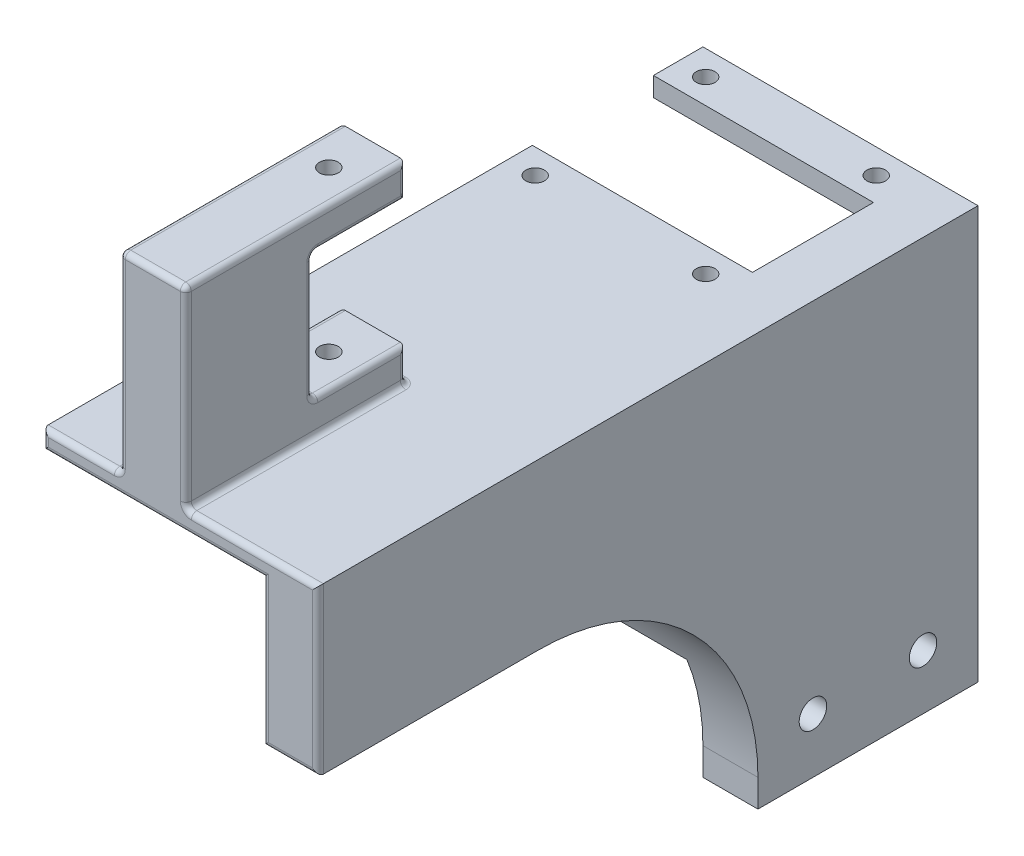
SolidWorks part; units mm, degrees
ref_plane "Front Plane" through (0, 0, 0) normal (0, 0, 1) x (1, 0, 0)
ref_plane "Top Plane" through (0, 0, 0) normal (0, 1, 0) x (1, 0, 0)
ref_plane "Right Plane" through (0, 0, 0) normal (1, 0, 0) x (0, 0, -1)
sketch "Sketch1" plane through (0, 0, 0) normal (1, 0, 0) x (0, 0, -1)
  line L0 (0, 27.5) -> (0, -27.5) construction
  line L5 (-20, 55) -> (20, 55)
  line L6 (-20, 55) -> (-20, 0)
  line L7 (-20, 0) -> (20, 0)
  line L8 (20, 55) -> (20, 0)
  line L9 (-20, 55) -> (20, 0) construction
  line L10 (-20, 0) -> (20, 55) construction
  line L11 (27.5, 0) -> (-27.5, 0) construction
  line L13 (-20, -20) -> (20, -20)
  line L14 (-20, -20) -> (-20, 0)
  line L15 (-20, 0) -> (20, 0)
  line L16 (20, -20) -> (20, 0)
  line L17 (-20, -20) -> (20, 0) construction
  line L18 (-20, 0) -> (20, -20) construction
  line L19 (10, -15) -> (-10, -15) construction
  line L20 (10, -15) -> (10, -5) construction
  line L21 (10, -5) -> (-10, -5) construction
  line L22 (-10, -15) -> (-10, -5) construction
  line L23 (10, -15) -> (-10, -5) construction
  line L24 (10, -5) -> (-10, -15) construction
  circle A0 centre (-10, -10) radius 2.5
  circle A1 centre (10, -10) radius 2.5
  point P1 (0, 27.5)
  point P10 (0, -10)
  point P11 (0, -10)
  dimension "D5" = 5
  dimension "D1" = 55
  dimension "D2" = 40
  dimension "D3" = 20
  dimension "D4" = 20
extrude "Boss-Extrude1" add sketch "Sketch1" along normal blind 10 contours L8 L5 L6 L7 | L13 L16 L7 L14 A1 A0
sketch "Sketch3" plane through (0, 0, 0) normal (-1, 0, 0) x (0, 0, 1)
  line L0 (20, 55) -> (20, -20) construction
  line L1 (-20, 10) -> (20, 10)
  line L2 (-20, 10) -> (-20, 0)
  line L3 (-20, 0) -> (20, 0)
  line L4 (20, 10) -> (20, 0)
  line L5 (-20, 10) -> (20, 0) construction
  line L6 (-20, 0) -> (20, 10) construction
  dimension "D1" = 10
extrude "Boss-Extrude2" add sketch "Sketch3" along normal blind 40
sketch "Sketch4" plane through (0, 0, 0) normal (-1, 0, 0) x (0, 0, 1)
  line L13 (-20, 55) -> (-11, 55)
  line L14 (-20, 55) -> (-20, 51.5)
  line L15 (-20, 51.5) -> (-11, 51.5)
  line L16 (-11, 55) -> (-11, 51.5)
  dimension "D1" = 9
  dimension "D2" = 3.5
extrude "Boss-Extrude3" add sketch "Sketch4" along normal blind 40
sketch "Sketch5" plane through (0, 55, 0) normal (0, 1, 0) x (1, 0, 0)
  line L1 (-40, 20) -> (-35, 20) construction
  line L2 (-40, 20) -> (-40, 15.5) construction
  line L3 (-40, 15.5) -> (-35, 15.5) construction
  line L4 (-35, 20) -> (-35, 15.5) construction
  line L5 (10, 20) -> (-40, 20) construction
  line L7 (1, 20) -> (-4, 20) construction
  line L8 (1, 20) -> (1, 15.5) construction
  line L9 (1, 15.5) -> (-4, 15.5) construction
  line L10 (-4, 20) -> (-4, 15.5) construction
  circle A0 centre (-35, 15.5) radius 1.7
  circle A1 centre (-4, 15.5) radius 1.7
  dimension "D3" = 3.4
  dimension "D7" = 3.4
  dimension "D1" = 5
  dimension "D2" = 4.5
  dimension "D4" = 4.5
  dimension "D5" = 5
  dimension "D6" = 31
extrude "Cut-Extrude1" cut sketch "Sketch5" against normal up to next (3.5 mm away)
mirror "Mirror2" about plane through (0, 0, 0) normal (0, 0, 1) of "Cut-Extrude1", "Boss-Extrude3"
sketch "Sketch7" plane through (0, 0, 20) normal (0, 0, 1) x (1, 0, 0)
  line L0 (0, -22) -> (0, 22) construction
  line L1 (-40, 55) -> (0, 55)
  line L2 (-40, 55) -> (-40, 51.5)
  line L3 (-40, 51.5) -> (0, 51.5)
  line L4 (0, 55) -> (0, 51.5)
  line L5 (-20, 51.5) -> (-20, 55) construction
  line L6 (-40, 53.25) -> (0, 53.25) construction
  line L7 (-40, 51.5) -> (0, 51.5) construction
  line L8 (10, 55) -> (10, -20) construction
  line L9 (0, 55) -> (10, 55)
  line L10 (0, 55) -> (0, 25)
  line L11 (0, 25) -> (10, 25)
  line L12 (10, 55) -> (10, 25)
  line L13 (5, 25) -> (5, 55) construction
  line L14 (0, 40) -> (10, 40) construction
  point P199 (5, 40)
  point P296 (-20, 53.25)
  line M2 (10, 55) -> (-40, 55)
  line M3 (-40, 55) -> (-40, 51.5)
  line M4 (-40, 51.5) -> (0, 51.5)
  line M5 (0, 51.5) -> (0, 10)
  line M11 (10, -20) -> (10, 55)
  dimension "D1" = 30
extrude "Boss-Extrude4" add sketch "Sketch7" along normal blind 80 contours L4 M2 M3 M4 | L11 L4 M5 M11 M2
sketch "Sketch8" plane through (0, 55, 0) normal (0, 1, 0) x (1, 0, 0)
  line L0 (10, -100) -> (-40, -100) construction
  line L1 (-26, -100) -> (-14, -100)
  line L2 (-26, -100) -> (-26, -60)
  line L3 (-26, -60) -> (-14, -60)
  line L4 (-14, -100) -> (-14, -60)
  line L5 (-20, -60) -> (-20, -100) construction
  line L6 (-26, -80) -> (-14, -80) construction
  line L7 (-40, -11) -> (-40, -100) construction
  line L8 (0, -22) -> (0, 22) construction
  point P100 (-20, -80)
  dimension "D1" = 12
  dimension "D2" = 40
extrude "Boss-Extrude5" add sketch "Sketch8" along normal blind 35
sketch "Sketch9" plane through (0, 0, 60) normal (0, 0, -1) x (-1, 0, 0)
  line L0 (14, 90) -> (14, 55) construction
  line L1 (14, 84) -> (26, 84)
  line L2 (14, 84) -> (14, 61)
  line L3 (14, 61) -> (26, 61)
  line L4 (26, 84) -> (26, 61)
  line L5 (20, 61) -> (20, 84) construction
  line L6 (14, 72.5) -> (26, 72.5) construction
  line L7 (26, 90) -> (26, 55) construction
  line L8 (14, 90) -> (26, 90) construction
  line L9 (-10, 55) -> (40, 55) construction
  point P172 (20, 72.5)
  dimension "D1" = 6
  dimension "D2" = 6
extrude "Cut-Extrude2" cut sketch "Sketch9" against normal blind 17
sketch "Sketch10" plane through (0, 90, 0) normal (0, 1, 0) x (1, 0, 0)
  line L0 (-20, -1038.2105) -> (-20, 48961.7895) construction
  line L1 (-26, -60) -> (-26, -100) construction
  line L2 (-14, -100) -> (-14, -60) construction
  line L4 (-14, -60) -> (-26, -60) construction
  circle A0 centre (-20, -68) radius 1.7
  dimension "D1" = 3.4
  dimension "D2" = 8
extrude "Cut-Extrude3" cut sketch "Sketch10" against normal up to surface (38.5 mm away) and the other way through all contours A0 up to face at (-35, 51.5, 13.8)
fillet "Fillet1" radius 1 27 edges at (-33, 55, 100) (-26, 55, 80) (-26, 87, 60) (-26, 72.5, 100) (-14, 55, 80) (-14, 72.5, 100) (-20, 55, 60) (-14, 87, 60) (-26, 90, 80) (-20, 90, 100) (-14, 90, 80) (-26, 58, 60) (-14, 58, 60) (-14, 72.5, 77) (-14, 61, 68.5) (-20, 84, 77) (-14, 84, 68.5) (-26, 72.5, 77) (-26, 84, 68.5) (-20, 61, 77) (-26, 61, 68.5) (-20, 51.5, 100) (0, 38.25, 100) (5, 25, 100) (10, 40, 100) (-2, 55, 100) (-40, 53.25, 100)
fillet "Fillet2" radius 40 1 edges at (5, 25, 20)
